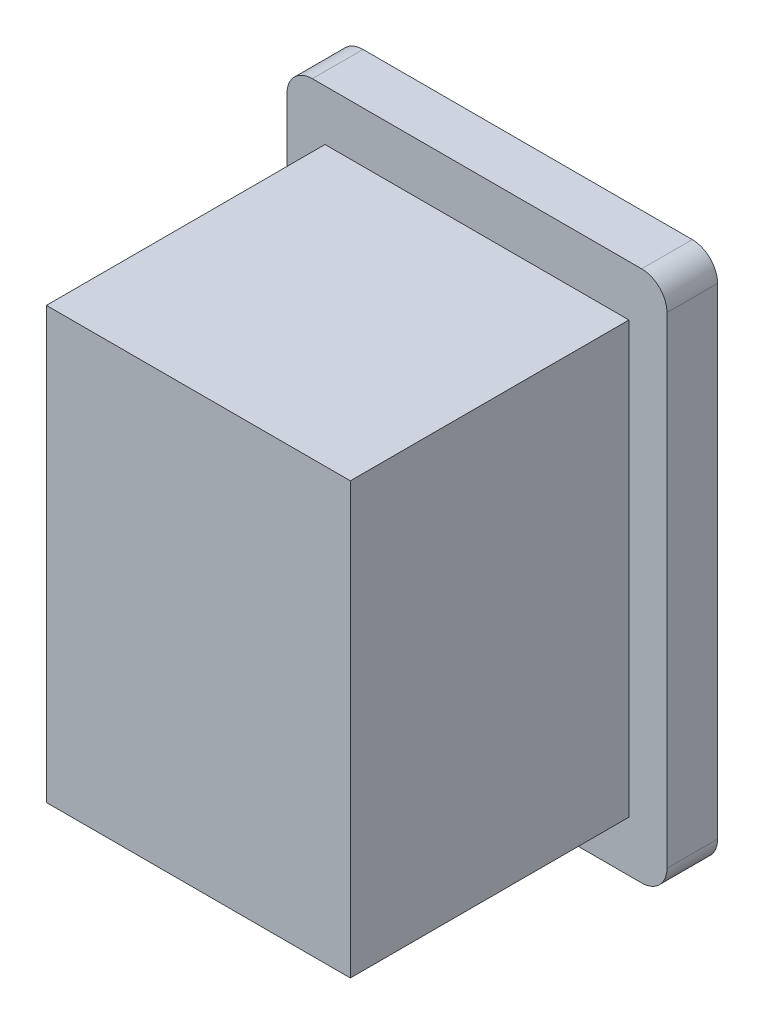
SolidWorks part; units mm, degrees
ref_plane "Front" through (0, 0, 0) normal (0, 0, 1) x (1, 0, 0)
ref_plane "Top" through (0, 0, 0) normal (0, 1, 0) x (1, 0, 0)
ref_plane "Right" through (0, 0, 0) normal (1, 0, 0) x (0, 0, -1)
sketch "Sketch1" plane through (0, 0, 0) normal (0, 0, 1) x (1, 0, 0)
  line L1 (-6, 8.5) -> (6, 8.5)
  line L2 (-6, 8.5) -> (-6, -8.5)
  line L3 (-6, -8.5) -> (6, -8.5)
  line L4 (6, 8.5) -> (6, -8.5)
  line L5 (-6, 8.5) -> (6, -8.5) construction
  line L6 (-6, -8.5) -> (6, 8.5) construction
  point P0 (0, 0)
  dimension "D1" = 17
  dimension "D2" = 12
extrude "Boss-Extrude1" add sketch "Sketch1" along normal blind 13
sketch "Sketch2" plane through (0, 0, 0) normal (0, 0, 1) x (1, 0, 0)
  line L1 (7.5, -10.5) -> (-7.5, -10.5)
  line L2 (7.5, -10.5) -> (7.5, 10.5)
  line L3 (7.5, 10.5) -> (-7.5, 10.5)
  line L4 (-7.5, -10.5) -> (-7.5, 10.5)
  line L5 (7.5, -10.5) -> (-7.5, 10.5) construction
  line L6 (7.5, 10.5) -> (-7.5, -10.5) construction
  point P0 (0, 0)
  dimension "D1" = 15
  dimension "D2" = 21
extrude "Boss-Extrude2" add sketch "Sketch2" along normal blind 2
fillet "Fillet1" radius 1 4 edges at (-7.5, -10.5, 1) (7.5, -10.5, 1) (-7.5, 10.5, 1) (7.5, 10.5, 1)
